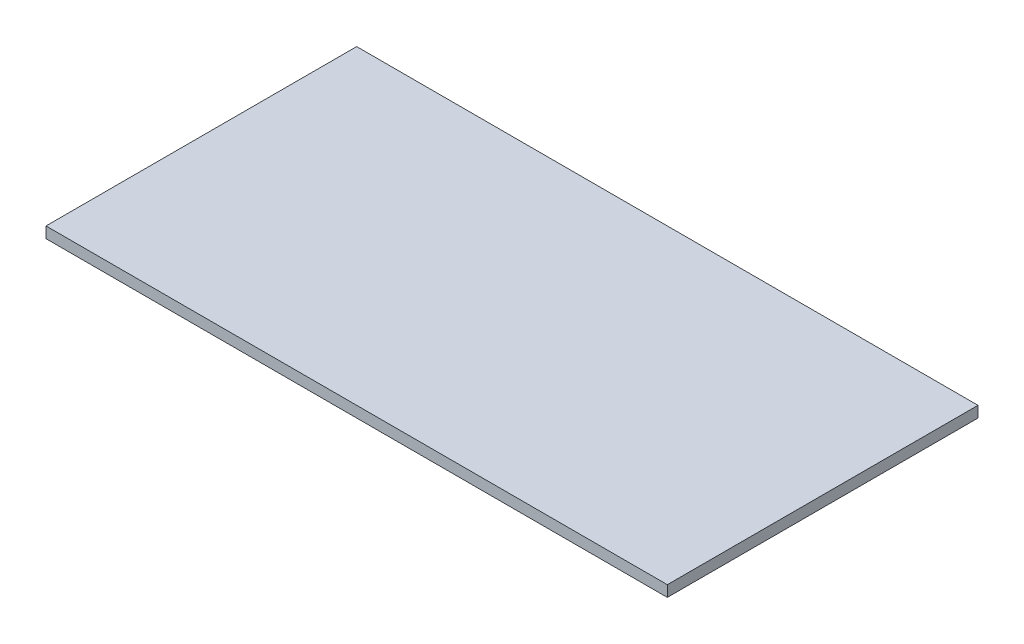
SolidWorks part; units mm, degrees
ref_plane "Front Plane" through (0, 0, 0) normal (0, 0, 1) x (1, 0, 0)
ref_plane "Top Plane" through (0, 0, 0) normal (0, 1, 0) x (1, 0, 0)
ref_plane "Right Plane" through (0, 0, 0) normal (1, 0, 0) x (0, 0, -1)
sketch "Sketch1" plane through (0, 0, 0) normal (0, 1, 0) x (1, 0, 0)
  line L1 (-38.5061, 20.2134) -> (51.4939, 20.2134)
  line L2 (-38.5061, 20.2134) -> (-38.5061, -24.7866)
  line L3 (-38.5061, -24.7866) -> (51.4939, -24.7866)
  line L4 (51.4939, 20.2134) -> (51.4939, -24.7866)
  dimension "D1" = 90
  dimension "D2" = 45
extrude "Boss-Extrude1" add sketch "Sketch1" along normal blind 1.6
